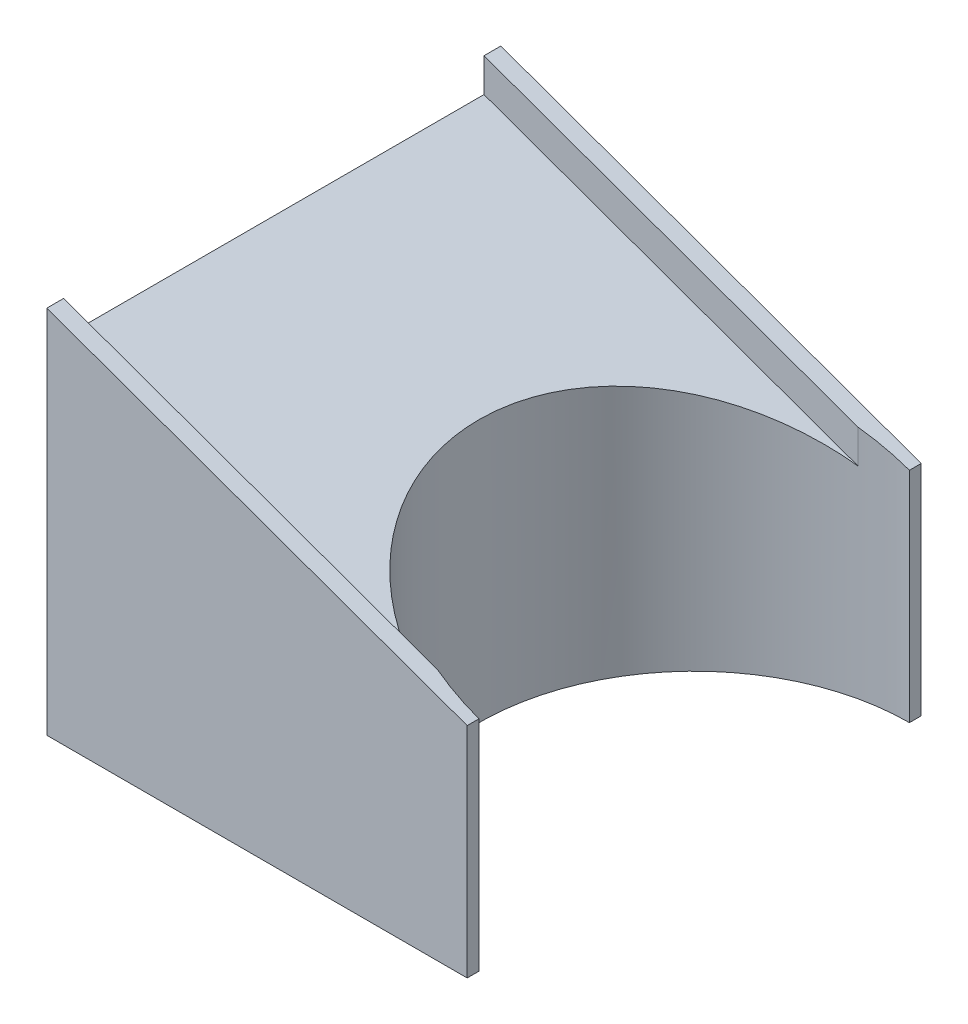
SolidWorks part; units mm, degrees
material "ABS"
ref_plane "Front" through (0, 0, 0) normal (0, 0, 1) x (1, 0, 0)
ref_plane "Top" through (0, 0, 0) normal (0, 1, 0) x (1, 0, 0)
ref_plane "Right" through (0, 0, 0) normal (1, 0, 0) x (0, 0, -1)
sketch "Sketch2" plane through (0, 0, 0) normal (0, 0, 1) x (1, 0, 0)
  line L0 (0, 0) -> (0, 100)
  line L2 (0, 100) -> (125, 55)
  line L3 (125, 55) -> (125, 0)
  line L4 (125, 0) -> (0, 0)
  point P3 (99.1131, 113.2885)
  point P7 (0, 0)
  dimension "D1" = 55
  dimension "125" = 125
  dimension "D3" = 100
extrude "Boss-Extrude1" add sketch "Sketch2" along normal mid plane 125
sketch "Sketch4" plane through (0, 0, 62.5) normal (0, 0, 1) x (1, 0, 0)
  line L18 (0, 0) -> (0, 110)
  line L19 (0, 110) -> (125, 65)
  line L20 (125, 65) -> (125, 0)
  line L25 (125, 0) -> (0, 0)
  line L26 (125, 0) -> (125, 55) construction
  line L27 (125, 55) -> (0, 100) construction
  point P8 (0, 100)
  dimension "D1" = 10
extrude "Boss-Extrude2" add sketch "Sketch4" along normal blind 5
mirror "Mirror1" about plane through (0, 0, 0) normal (0, 0, 1) of "Boss-Extrude2"
sketch "Sketch3" plane through (0, 0, 0) normal (0, -1, 0) x (1, 0, 0)
  line L0 (125, 67.5) -> (125, -67.5) construction
  circle A0 centre (125, 0) radius 64
  dimension "D1" = 128
extrude "Cut-Extrude1" cut sketch "Sketch3" against normal through all
sketch "Sketch5" plane through (0, 0, 0) normal (-1, 0, 0) x (0, 0, 1)
  line L0 (0, 100) -> (0, 0) construction
  line L1 (62.5, 100) -> (-62.5, 100) construction
  line L2 (67.5, 0) -> (-67.5, 0) construction
  point P6 (0, 20)
  point P7 (0, 55)
  dimension "D1" = 20
  dimension "D2" = 55
hole_wizard "#10 Clearance Hole1" positions "Sketch6" profile "Sketch7" hole size "#10" standard "ANSI Inch"
sketch "Sketch6" plane through (0, 0, 0) normal (-1, 0, 0) x (0, 0, 1)
  point P0 (0, 55)
  point P3 (0, 20)
sketch "Sketch7" plane through (0, 55, 0) normal (0, 1, 0) x (0, 0, 1)
  line L0 (0, 0) -> (0, 14.1346)
  line L1 (0, 14.1346) -> (2.3876, 12.7)
  line L2 (2.3876, 12.7) -> (2.3876, 0)
  line L5 (2.3876, 0) -> (0, 0)
  line L10 (0, 14.1346) -> (-2.3876, 12.7) construction
  line L11 (0, -6.35) -> (0, 107.95) construction
  dimension "Hole Dia." = 4.7752
  dimension "Hole Depth" = 12.7
  dimension "Drill Angle" = 118
